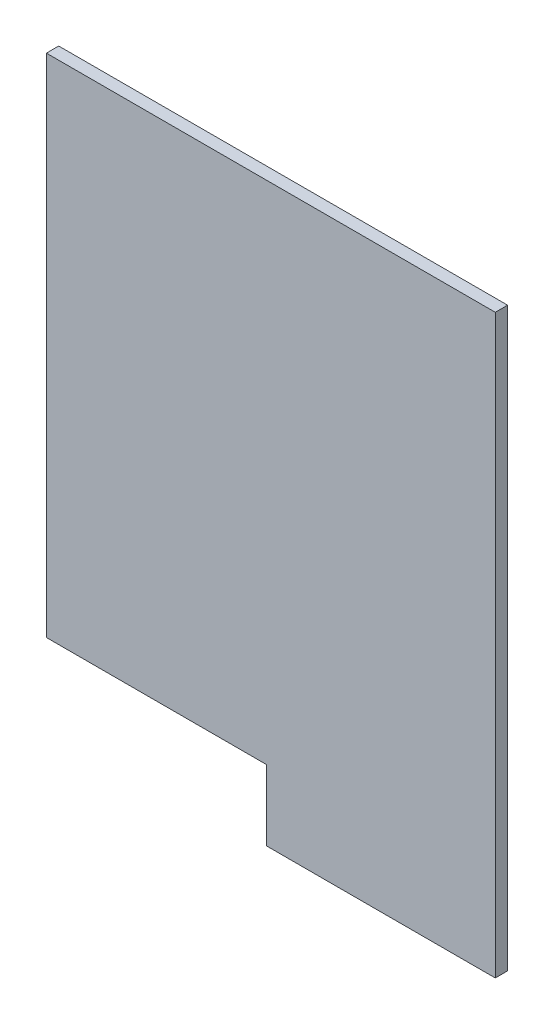
SolidWorks part; units mm, degrees
ref_plane "Plano frontal" through (0, 0, 0) normal (0, 0, 1) x (1, 0, 0)
ref_plane "Plano superior" through (0, 0, 0) normal (0, 1, 0) x (1, 0, 0)
ref_plane "Plano direito" through (0, 0, 0) normal (1, 0, 0) x (0, 0, -1)
sketch "Esboço1" plane through (0, 0, 0) normal (0, 0, 1) x (1, 0, 0)
  line L0 (0, 0) -> (0, -5750)
  line L1 (0, -5750) -> (2500, -5750)
  line L2 (2500, -5750) -> (2500, -6550)
  line L3 (2500, -6550) -> (5100, -6550)
  line L4 (5100, -6550) -> (5100, 0)
  line L5 (5100, 0) -> (0, 0)
  dimension "D1" = 5100
  dimension "D2" = 6550
  dimension "D3" = 2600
  dimension "D4" = 5750
extrude "Ressalto-extrusão1" add sketch "Esboço1" along normal blind 140
